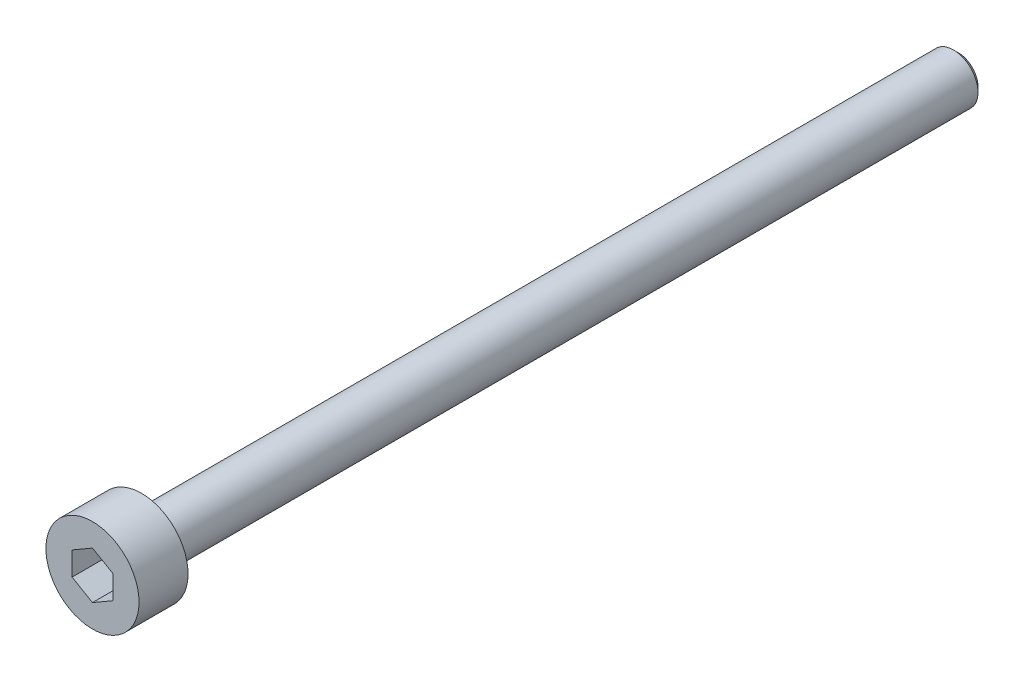
SolidWorks part; units mm, degrees
ref_plane "Front Plane" through (0, 0, 0) normal (0, 0, 1) x (1, 0, 0)
ref_plane "Top Plane" through (0, 0, 0) normal (0, 1, 0) x (1, 0, 0)
ref_plane "Right Plane" through (0, 0, 0) normal (1, 0, 0) x (0, 0, -1)
sketch "Sketch1" plane through (0, 0, 0) normal (0, 0, 1) x (1, 0, 0)
  circle A0 centre (0, 0) radius 2.85
  dimension "D1" = 5.7
extrude "Boss-Extrude1" add sketch "Sketch1" along normal blind 3
sketch "Sketch2" plane through (0, 0, 0) normal (0, 0, -1) x (-1, 0, 0)
  circle A0 centre (0, 0) radius 1.5
  dimension "D1" = 3
extrude "Boss-Extrude2" add sketch "Sketch2" along normal blind 50
chamfer "Chamfer1" distance 0.3 angle 45 1 edges at (-1.5, 0, -50)
sketch "Sketch3" plane through (0, 0, 3) normal (0, 0, 1) x (1, 0, 0)
  line L1 (0, 1.4434) -> (-1.25, 0.7217)
  line L2 (-1.25, 0.7217) -> (-1.25, -0.7217)
  line L3 (-1.25, -0.7217) -> (0, -1.4434)
  line L4 (0, -1.4434) -> (1.25, -0.7217)
  line L5 (1.25, -0.7217) -> (1.25, 0.7217)
  line L6 (1.25, 0.7217) -> (0, 1.4434)
  circle A0 centre (0, 0) radius 1.25 construction
  dimension "D1" = 2.5
extrude "Cut-Extrude1" cut sketch "Sketch3" against normal blind 2
